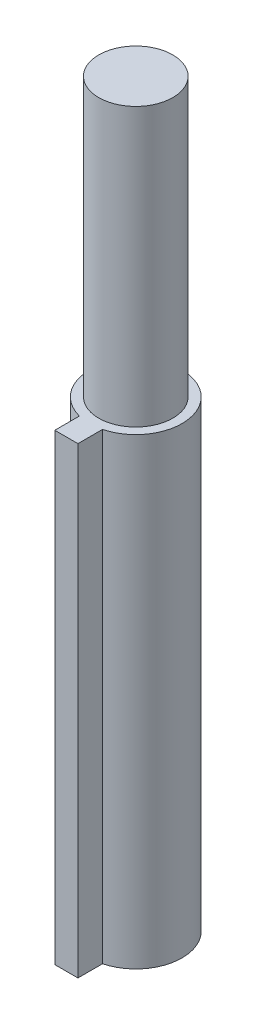
SolidWorks part; units mm, degrees
ref_plane "Front Plane" through (0, 0, 0) normal (0, 0, 1) x (1, 0, 0)
ref_plane "Top Plane" through (0, 0, 0) normal (0, 1, 0) x (1, 0, 0)
ref_plane "Right Plane" through (0, 0, 0) normal (1, 0, 0) x (0, 0, -1)
sketch "Sketch1" plane through (0, 0, 0) normal (0, 1, 0) x (1, 0, 0)
  circle A0 centre (0, 0) radius 5
  dimension "D1" = 10
extrude "Boss-Extrude1" add sketch "Sketch1" along normal blind 50
sketch "Sketch2" plane through (0, 50, 0) normal (0, 1, 0) x (1, 0, 0)
  circle A0 centre (0, 0) radius 4
  dimension "D1" = 8
extrude "Boss-Extrude2" add sketch "Sketch2" along normal blind 30
sketch "Sketch3" plane through (0, 0, 0) normal (0, -1, 0) x (1, 0, 0)
  line L1 (1.25, 7.5) -> (-1.25, 7.5)
  line L2 (1.25, 7.5) -> (1.25, 2.5)
  line L3 (1.25, 2.5) -> (-1.25, 2.5)
  line L4 (-1.25, 7.5) -> (-1.25, 2.5)
  line L5 (1.25, 7.5) -> (-1.25, 2.5) construction
  line L6 (1.25, 2.5) -> (-1.25, 7.5) construction
  circle A0 centre (0, 0) radius 5 construction
  point P0 (0, 5)
  dimension "D1" = 2.5
  dimension "D2" = 5
extrude "Boss-Extrude3" add sketch "Sketch3" against normal up to surface (50 mm away) up to face at (0, 50, 4)
